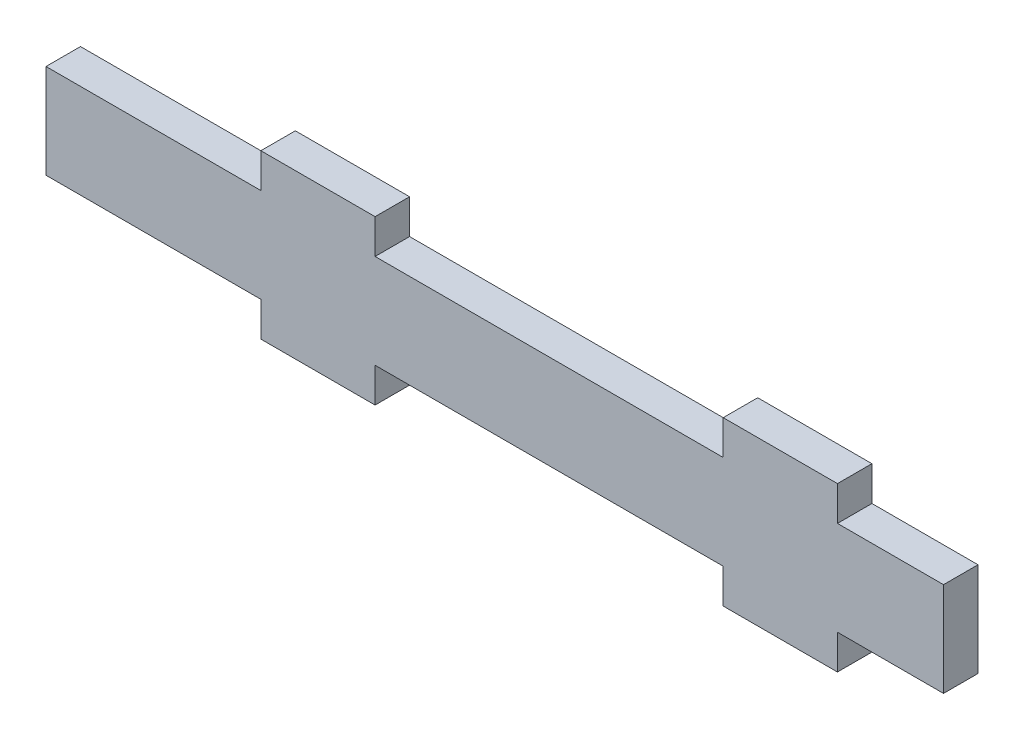
SolidWorks part; units mm, degrees
ref_plane "Front Plane" through (0, 0, 0) normal (0, 0, 1) x (1, 0, 0)
ref_plane "Top Plane" through (0, 0, 0) normal (0, 1, 0) x (1, 0, 0)
ref_plane "Right Plane" through (0, 0, 0) normal (1, 0, 0) x (0, 0, -1)
sketch "Sketch1" plane through (0, 0, 0) normal (0, 0, 1) x (1, 0, 0)
  line L1 (0, 0) -> (82.5, 0)
  line L2 (0, 0) -> (0, 8.66)
  line L3 (0, 8.66) -> (82.5, 8.66)
  line L4 (82.5, 0) -> (82.5, 8.66)
  line L5 (19.75, 0) -> (30.25, 0)
  line L6 (19.75, 0) -> (19.75, -3.17)
  line L7 (19.75, -3.17) -> (30.25, -3.17)
  line L8 (30.25, 0) -> (30.25, -3.17)
  line L9 (19.75, 8.66) -> (30.25, 8.66)
  line L10 (19.75, 8.66) -> (19.75, 11.83)
  line L11 (19.75, 11.83) -> (30.25, 11.83)
  line L12 (30.25, 8.66) -> (30.25, 11.83)
  line L13 (62.25, 8.66) -> (72.75, 8.66)
  line L14 (62.25, 8.66) -> (62.25, 11.83)
  line L15 (62.25, 11.83) -> (72.75, 11.83)
  line L16 (72.75, 8.66) -> (72.75, 11.83)
  line L17 (62.25, 0) -> (72.75, 0)
  line L18 (62.25, 0) -> (62.25, -3.17)
  line L19 (62.25, -3.17) -> (72.75, -3.17)
  line L20 (72.75, 0) -> (72.75, -3.17)
  point P21 (30.25, 10.245)
  point P22 (25, 11.83)
  point P23 (67.5, 11.83)
  dimension "D1" = 32
  dimension "D2" = 25
  dimension "D3" = 15
  dimension "D4" = 10.5
  dimension "D5" = 3.17
  dimension "D6" = 15
  dimension "D7" = 82.5
extrude "Boss-Extrude1" add sketch "Sketch1" along normal blind 3.17 contours L1 L4 L3 L2 | L3 L12 L11 L10 | L3 L16 L15 L14 | L7 L8 L5 L6 | L19 L20 L17 L18
